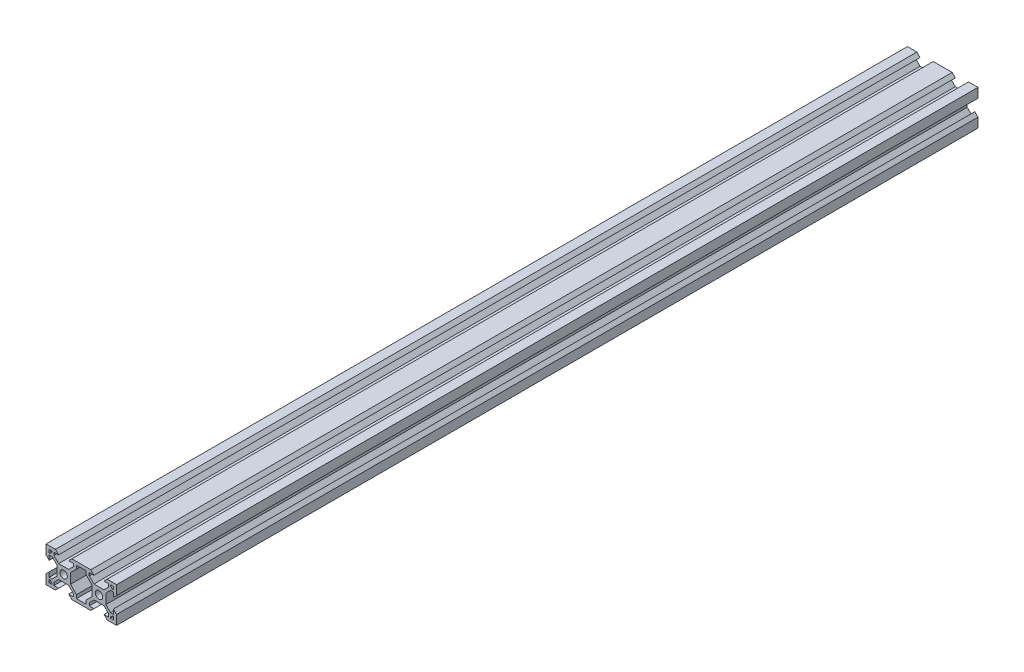
SolidWorks part; units mm, degrees
ref_plane "Front Plane" through (0, 0, 0) normal (0, 0, 1) x (1, 0, 0)
ref_plane "Top Plane" through (0, 0, 0) normal (0, 1, 0) x (1, 0, 0)
ref_plane "Right Plane" through (0, 0, 0) normal (1, 0, 0) x (0, 0, -1)
sketch "Sketch1" plane through (0, 0, 0) normal (0, 0, 1) x (1, 0, 0)
  line L0 (0, 0) -> (0, 5.36)
  line L1 (0, 20) -> (5.36, 20)
  line L3 (20, 0) -> (14.64, 0)
  line L4 (0, 10) -> (20, 10) construction
  line L5 (5.36, 0) -> (0, 0)
  line L6 (4.5007, 18.2) -> (7.16, 18.2)
  line L7 (17.3007, 3.76) -> (17.3007, 1.8)
  line L8 (15.4993, 1.8) -> (12.84, 1.8)
  line L9 (20, 0) -> (0, 0) construction
  line L10 (7.16, 1.8) -> (4.5007, 1.8)
  line L11 (15.4993, 3.44) -> (12.84, 6.0993)
  line L12 (4.5007, 16.56) -> (7.16, 13.9007)
  line L13 (13.9007, 12.84) -> (13.9007, 7.16)
  line L14 (12.84, 13.9007) -> (7.16, 13.9007)
  line L15 (6.0993, 12.84) -> (6.0993, 7.16)
  line L16 (7.16, 6.0993) -> (12.84, 6.0993)
  line L17 (4.5007, 16.56) -> (4.5007, 18.2)
  line L18 (3.44, 15.4993) -> (1.8, 15.4993)
  line L19 (4.5007, 3.44) -> (4.5007, 1.8)
  line L20 (3.44, 4.5007) -> (1.8, 4.5007)
  line L21 (15.4993, 3.44) -> (15.4993, 1.8)
  line L23 (17.3007, 1.8) -> (22.7007, 1.8)
  line L24 (15.4993, 16.56) -> (15.4993, 18.2)
  line L25 (7.16, 18.2) -> (5.36, 20)
  line L26 (12.84, 1.8) -> (14.64, 0)
  line L27 (7.16, 1.8) -> (5.36, 0)
  line L28 (12.84, 18.2) -> (14.64, 20)
  line L29 (1.8, 7.16) -> (0, 5.36)
  line L30 (1.8, 12.84) -> (0, 14.64)
  line L31 (22.7007, 1.8) -> (22.7007, 3.76)
  line L32 (17.3007, 16.24) -> (17.3007, 18.2)
  line L33 (17.3007, 18.2) -> (22.6993, 18.2)
  line L34 (22.6993, 18.2) -> (22.6993, 16.24)
  line L35 (38.2013, 12.8423) -> (40.001, 14.6427)
  line L36 (38.2024, 7.1623) -> (40.0028, 5.3627)
  line L37 (27.16, 18.2) -> (25.36, 20)
  line L38 (32.84, 1.8) -> (34.64, 0)
  line L39 (27.16, 1.8) -> (25.36, 0)
  line L40 (32.84, 18.2) -> (34.64, 20)
  line L41 (24.5013, 16.5597) -> (24.5009, 18.2)
  line L42 (1.8, 18.2) -> (3.4307, 18.2)
  line L43 (3.4307, 18.2) -> (3.4307, 17.63)
  line L44 (24.5038, 3.4397) -> (24.5041, 1.8)
  line L45 (36.5629, 4.5027) -> (38.2029, 4.503)
  line L46 (35.5025, 3.4418) -> (35.5028, 1.8)
  line L47 (36.5608, 15.5014) -> (38.2008, 15.5017)
  line L48 (35.4999, 16.5618) -> (35.4996, 18.2)
  line L49 (32.8426, 6.1006) -> (27.1626, 6.0995)
  line L50 (33.902, 12.8415) -> (33.9031, 7.1615)
  line L51 (27.1611, 13.9009) -> (32.8411, 13.902)
  line L52 (26.1007, 12.84) -> (26.1007, 7.16)
  line L53 (1.8, 4.5007) -> (1.8, 7.16)
  line L54 (24.5038, 3.4397) -> (27.1626, 6.0995)
  line L55 (35.5025, 3.4418) -> (32.8426, 6.1006)
  line L56 (36.5629, 4.5027) -> (33.9031, 7.1615)
  line L57 (24.5041, 1.8) -> (27.16, 1.8)
  line L58 (3.4307, 17.63) -> (2.37, 16.5693)
  line L59 (3.44, 4.5007) -> (6.0993, 7.16)
  line L60 (35.4996, 18.2) -> (32.84, 18.2)
  line L61 (20, 0) -> (25.36, 0)
  line L62 (39.9999, 20) -> (34.64, 20)
  line L63 (40.0038, 0) -> (40.0028, 5.3627)
  line L64 (1.8, 12.84) -> (1.8, 15.4993)
  line L65 (1.8, 1.8) -> (1.8, 18.2) construction
  line L66 (0, 14.64) -> (0, 20)
  line L67 (0, 0) -> (0, 20) construction
  line L68 (14.64, 20) -> (20, 20)
  line L69 (0, 20) -> (20, 20) construction
  line L70 (12.84, 18.2) -> (15.4993, 18.2)
  line L71 (1.8, 18.2) -> (18.2, 18.2) construction
  line L72 (25.36, 20) -> (20, 20)
  line L73 (27.16, 18.2) -> (24.5009, 18.2)
  line L74 (38.2013, 12.8423) -> (38.2008, 15.5017)
  line L75 (40.001, 14.6427) -> (39.9999, 20)
  line L76 (32.84, 1.8) -> (35.5028, 1.8)
  line L77 (34.64, 0) -> (40.0038, 0)
  line L78 (38.2029, 4.503) -> (38.2024, 7.1623)
  line L79 (35.4999, 16.5618) -> (32.8411, 13.902)
  line L80 (4.5007, 3.44) -> (7.16, 6.0993)
  line L81 (2.37, 16.5693) -> (1.8, 16.5693)
  line L82 (18.2, 1.8) -> (1.8, 1.8) construction
  line L83 (18.2, 18.2) -> (18.2, 1.8) construction
  line L84 (1.8, 16.5693) -> (1.8, 18.2)
  line L85 (20, 20) -> (20, 0) construction
  line L86 (1.8, 3.4307) -> (1.8, 1.8)
  line L87 (2.37, 3.4307) -> (1.8, 3.4307)
  line L88 (3.4307, 2.37) -> (2.37, 3.4307)
  line L89 (3.4307, 1.8) -> (3.4307, 2.37)
  line L90 (1.8, 1.8) -> (3.4307, 1.8)
  line L91 (13.9007, 7.16) -> (17.3007, 3.76)
  line L92 (20, 20) -> (20, -0.3542) construction
  line L93 (38.2, 1.8) -> (36.5693, 1.8)
  line L94 (36.5693, 1.8) -> (36.5693, 2.37)
  line L95 (36.5693, 2.37) -> (37.63, 3.4307)
  line L96 (37.63, 3.4307) -> (38.2, 3.4307)
  line L97 (38.2, 3.4307) -> (38.2, 1.8)
  line L98 (38.2, 16.5693) -> (38.2, 18.2)
  line L99 (37.63, 16.5693) -> (38.2, 16.5693)
  line L100 (36.5693, 17.63) -> (37.63, 16.5693)
  line L101 (36.5693, 18.2) -> (36.5693, 17.63)
  line L102 (38.2, 18.2) -> (36.5693, 18.2)
  line L103 (6.0993, 12.84) -> (3.44, 15.4993)
  line L104 (13.9007, 12.84) -> (17.3007, 16.24)
  line L105 (12.84, 13.9007) -> (15.4993, 16.56)
  line L106 (33.902, 12.8415) -> (36.5608, 15.5014)
  line L108 (27.1611, 13.9009) -> (24.5013, 16.5597)
  line L109 (26.1007, 12.84) -> (22.6993, 16.24)
  line L110 (26.1007, 7.16) -> (22.7007, 3.76)
  circle A0 centre (10, 10) radius 2.1
  circle A1 centre (30, 10) radius 2.1
  point P14 (17.3007, 3.76)
  point P81 (0, 0)
  point P82 (0, 0)
  point P112 (17.3007, 1.8)
  dimension "D3" = 4.2
  dimension "D1" = 20
  dimension "D2" = 20
  dimension "D5" = 5.4
  dimension "D7" = 1.07
  dimension "D8" = 45
  dimension "D9" = 1.5
  dimension "D10" = 4.5007
  dimension "D11" = 5.68
  dimension "D12" = 5.68
  dimension "D13" = 5.68
  dimension "D14" = 5.68
  dimension "D15" = 1.64
  dimension "D16" = 1.64
  dimension "D17" = 1.64
  dimension "D18" = 1.64
  dimension "D19" = 1.64
  dimension "D20" = 15.4993
  dimension "D21" = 1.07
  dimension "D22" = 1.64
  dimension "D23" = 45
  dimension "D24" = 45
  dimension "D25" = 1.5
  dimension "D26" = 45
  dimension "D27" = 45
  dimension "D28" = 45
  dimension "D4" = 1.8
extrude "Boss-Extrude1" add sketch "Sketch1" against normal blind 488
